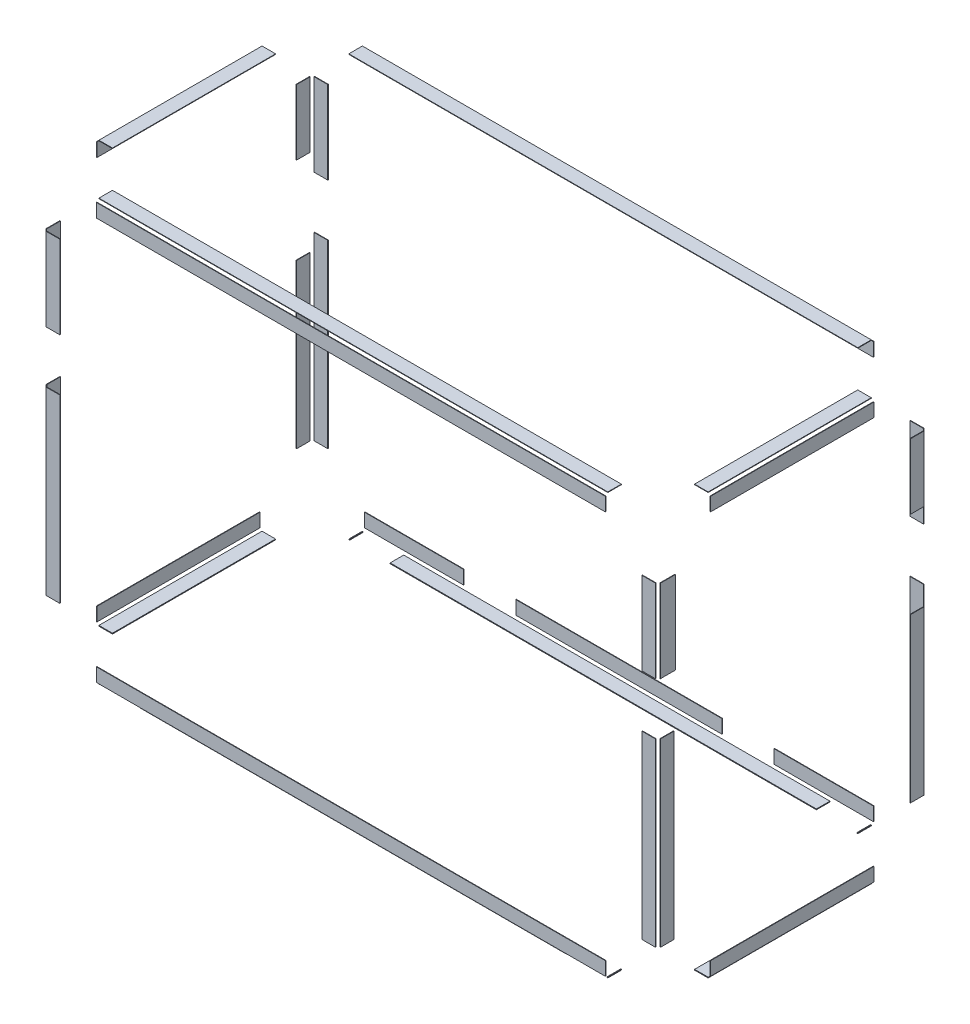
SolidWorks part; units mm, degrees
ref_plane "Front Plane" through (0, 0, 0) normal (0, 0, 1) x (1, 0, 0)
ref_plane "Top Plane" through (0, 0, 0) normal (0, 1, 0) x (1, 0, 0)
ref_plane "Right Plane" through (0, 0, 0) normal (1, 0, 0) x (0, 0, -1)
sketch "Sketch1" plane through (965.8572, 0, 0) normal (1, 0, 0) x (0, 0, -1)
  line L1 (-242.2862, 651.1987) -> (264.3978, 651.1987)
  line L2 (-242.2862, 651.1987) -> (-242.2862, 609.0982)
  line L3 (-242.2862, 609.0982) -> (264.3978, 609.0982)
  line L4 (264.3978, 651.1987) -> (264.3978, 609.0982)
  line L5 (378.0945, 495.4014) -> (420.195, 495.4014)
  line L6 (378.0945, 495.4014) -> (378.0945, 292.2639)
  line L7 (378.0945, 292.2639) -> (420.195, 292.2639)
  line L8 (420.195, 495.4014) -> (420.195, 292.2639)
  line L9 (-398.655, 495.4014) -> (-351.5479, 495.4014)
  line L10 (-398.655, 495.4014) -> (-398.655, 238.2889)
  line L11 (-398.655, 238.2889) -> (-351.5479, 238.2889)
  line L12 (-351.5479, 495.4014) -> (-351.5479, 238.2889)
  line L13 (-398.0835, 76.3639) -> (-355.983, 76.3639)
  line L14 (-398.0835, 76.3639) -> (-398.0835, -484.1046)
  line L15 (-398.0835, -484.1046) -> (-355.983, -484.1046)
  line L16 (-355.983, 76.3639) -> (-355.983, -484.1046)
  line L17 (-242.2862, -597.8013) -> (264.3978, -597.8013)
  line L18 (-242.2862, -597.8013) -> (-242.2862, -639.9018)
  line L19 (-242.2862, -639.9018) -> (264.3978, -639.9018)
  line L20 (264.3978, -597.8013) -> (264.3978, -639.9018)
  line L21 (378.0945, 22.3889) -> (420.195, 22.3889)
  line L22 (378.0945, 22.3889) -> (378.0945, -484.1046)
  line L23 (378.0945, -484.1046) -> (420.195, -484.1046)
  line L24 (420.195, 22.3889) -> (420.195, -484.1046)
extrude "Boss-Extrude1" add sketch "Sketch1" along normal blind 1.5875
sketch "Sketch2" plane through (0, 0, 404.2112) normal (0, 0, 1) x (1, 0, 0)
  line L1 (-776.5738, 605.6529) -> (-776.5738, 651.7702) construction
  line L2 (-776.5738, 651.1987) -> (803.9322, 651.1987)
  line L3 (-776.5738, 651.1987) -> (-776.5738, 609.0982)
  line L4 (-776.5738, 609.0982) -> (803.9322, 609.0982)
  line L9 (803.9322, 651.1987) -> (803.9322, 609.0982)
  line L10 (911.5012, 651.1987) -> (-884.1428, 651.1987) construction
  line L11 (803.9322, 651.7702) -> (803.9322, 605.6529) construction
  line L12 (911.5012, 609.0982) -> (-884.1428, 609.0982) construction
  line L15 (-776.5738, -640.4733) -> (-776.5738, -594.3561) construction
  line L16 (-776.5738, -597.8013) -> (803.9322, -597.8013)
  line L17 (-776.5738, -597.8013) -> (-776.5738, -639.9018)
  line L18 (-776.5738, -639.9018) -> (803.9322, -639.9018)
  line L20 (917.629, -646.0296) -> (917.629, 657.3264) construction
  line L21 (917.629, 495.4014) -> (959.7295, 495.4014)
  line L22 (917.629, 495.4014) -> (917.629, 238.2889)
  line L23 (917.629, 238.2889) -> (959.7295, 238.2889)
  line L24 (959.7295, 495.4014) -> (959.7295, 238.2889)
  line L25 (914.1837, 495.4014) -> (960.301, 495.4014) construction
  line L26 (960.301, 238.2889) -> (913.1939, 238.2889) construction
  line L27 (959.7295, -646.0296) -> (959.7295, 657.3264) construction
  line L28 (913.1939, 76.3639) -> (960.301, 76.3639) construction
  line L29 (917.629, 76.3639) -> (959.7295, 76.3639)
  line L30 (917.629, 76.3639) -> (917.629, -484.1046)
  line L31 (917.629, -484.1046) -> (959.7295, -484.1046)
  line L32 (959.7295, 76.3639) -> (959.7295, -484.1046)
  line L33 (960.301, -484.1046) -> (914.1837, -484.1046) construction
  line L35 (803.9322, -597.8013) -> (803.9322, -639.9018)
  line L36 (911.5012, -597.8013) -> (-884.1428, -597.8013) construction
  line L37 (911.5012, -639.9018) -> (-884.1428, -639.9018) construction
  line L38 (803.9322, -594.3561) -> (803.9322, -640.4733) construction
  line L54 (-932.9425, 76.3639) -> (-885.8354, 76.3639) construction
  line L55 (-932.371, 76.3639) -> (-890.2705, 76.3639)
  line L56 (-932.371, 76.3639) -> (-932.371, -484.1046)
  line L57 (-932.371, -484.1046) -> (-890.2705, -484.1046)
  line L58 (-890.2705, 76.3639) -> (-890.2705, -484.1046)
  line L59 (-932.371, -646.0296) -> (-932.371, 657.3264) construction
  line L60 (-890.2705, -646.0296) -> (-890.2705, 657.3264) construction
  line L61 (-886.8253, -484.1046) -> (-932.9425, -484.1046) construction
  line L62 (-932.9425, 495.4014) -> (-886.8253, 495.4014) construction
  line L63 (-932.371, 495.4014) -> (-890.2705, 495.4014)
  line L64 (-932.371, 495.4014) -> (-932.371, 238.2889)
  line L65 (-932.371, 238.2889) -> (-890.2705, 238.2889)
  line L66 (-890.2705, 495.4014) -> (-890.2705, 238.2889)
  line L67 (-885.8354, 238.2889) -> (-932.9425, 238.2889) construction
extrude "Boss-Extrude2" add sketch "Sketch2" along normal blind 1.5875 separate body
sketch "Sketch3" plane through (-938.4988, 0, 0) normal (-1, 0, 0) x (0, 0, 1)
  line L0 (242.2862, 651.1987) -> (242.2862, 609.0982) construction
  line L1 (-264.3978, 651.1987) -> (242.2862, 651.1987)
  line L2 (-264.3978, 651.1987) -> (-264.3978, 609.0982)
  line L3 (-264.3978, 609.0982) -> (242.2862, 609.0982)
  line L4 (242.2862, 651.1987) -> (242.2862, 609.0982)
  line L5 (242.2862, 609.0982) -> (242.2862, 651.1987) construction
  line L7 (355.983, 495.4014) -> (398.655, 495.4014)
  line L8 (355.983, 495.4014) -> (355.983, 238.2889)
  line L9 (355.983, 238.2889) -> (398.655, 238.2889)
  line L10 (398.655, 495.4014) -> (398.655, 238.2889)
  line L11 (355.983, 76.3639) -> (398.0835, 76.3639)
  line L12 (355.983, 76.3639) -> (355.983, -484.1046)
  line L13 (355.983, -484.1046) -> (398.0835, -484.1046)
  line L14 (398.0835, 76.3639) -> (398.0835, -484.1046)
  line L15 (-264.3978, -597.8013) -> (242.2862, -597.8013)
  line L16 (-264.3978, -597.8013) -> (-264.3978, -639.9018)
  line L17 (-264.3978, -639.9018) -> (242.2862, -639.9018)
  line L18 (242.2862, -597.8013) -> (242.2862, -639.9018)
  line L19 (-420.195, 22.3889) -> (-378.0945, 22.3889)
  line L20 (-420.195, 22.3889) -> (-420.195, -484.1046)
  line L21 (-420.195, -484.1046) -> (-378.0945, -484.1046)
  line L22 (-378.0945, 22.3889) -> (-378.0945, -484.1046)
  line L23 (-420.195, 495.4014) -> (-378.0945, 495.4014)
  line L24 (-420.195, 495.4014) -> (-420.195, 292.2639)
  line L25 (-420.195, 292.2639) -> (-378.0945, 292.2639)
  line L26 (-378.0945, 495.4014) -> (-378.0945, 292.2639)
extrude "Boss-Extrude3" add sketch "Sketch3" along normal blind 1.5875 separate body
sketch "Sketch5" plane through (0, 0, -426.3228) normal (0, 0, -1) x (-1, 0, 0)
  line L0 (-495.6417, 651.7702) -> (-495.6417, 604.6631) construction
  line L1 (-803.9322, 651.1987) -> (-495.6417, 651.1987)
  line L2 (-803.9322, 651.1987) -> (-803.9322, 609.0982)
  line L3 (-803.9322, 609.0982) -> (-495.6417, 609.0982)
  line L4 (-495.6417, 651.1987) -> (-495.6417, 609.0982)
  line L5 (-911.5012, 609.0982) -> (-441.8572, 609.0982) construction
  line L6 (-803.9322, 651.1987) -> (776.5738, 651.1987) construction
  line L7 (-333.7167, 651.1987) -> (306.3583, 651.1987)
  line L8 (-333.7167, 651.1987) -> (-333.7167, 609.0982)
  line L9 (-333.7167, 609.0982) -> (306.3583, 609.0982)
  line L10 (306.3583, 651.1987) -> (306.3583, 609.0982)
  line L11 (-333.7167, 604.6631) -> (-333.7167, 651.7702) construction
  line L12 (306.3583, 651.7702) -> (306.3583, 604.6631) construction
  line L13 (468.2833, 604.6631) -> (468.2833, 651.7702) construction
  line L14 (468.2833, 651.1987) -> (776.5738, 651.1987)
  line L15 (468.2833, 651.1987) -> (468.2833, 609.0982)
  line L16 (468.2833, 609.0982) -> (776.5738, 609.0982)
  line L17 (776.5738, 651.1987) -> (776.5738, 609.0982)
  line L18 (414.4988, 651.1987) -> (884.1428, 651.1987) construction
  line L19 (-803.9322, -597.8013) -> (776.5738, -597.8013) construction
  line L20 (890.2705, 495.4014) -> (932.371, 495.4014)
  line L21 (890.2705, 495.4014) -> (890.2705, 238.2889)
  line L22 (890.2705, 238.2889) -> (932.371, 238.2889)
  line L23 (932.371, 495.4014) -> (932.371, 238.2889)
  line L24 (890.2705, 76.3639) -> (932.371, 76.3639)
  line L25 (890.2705, 76.3639) -> (890.2705, -484.1046)
  line L26 (890.2705, -484.1046) -> (932.371, -484.1046)
  line L27 (932.371, 76.3639) -> (932.371, -484.1046)
  line L28 (468.2833, -597.8013) -> (776.5738, -597.8013)
  line L29 (468.2833, -597.8013) -> (468.2833, -639.9018)
  line L30 (468.2833, -639.9018) -> (776.5738, -639.9018)
  line L31 (776.5738, -597.8013) -> (776.5738, -639.9018)
  line L32 (468.2833, -640.4733) -> (468.2833, -593.3662) construction
  line L33 (-333.7167, -640.4733) -> (-333.7167, -593.3662) construction
  line L34 (-333.7167, -597.8013) -> (306.3583, -597.8013)
  line L35 (-333.7167, -597.8013) -> (-333.7167, -639.9018)
  line L36 (-333.7167, -639.9018) -> (306.3583, -639.9018)
  line L37 (306.3583, -597.8013) -> (306.3583, -639.9018)
  line L38 (776.5738, -639.9018) -> (-803.9322, -639.9018) construction
  line L39 (306.3583, -593.3662) -> (306.3583, -640.4733) construction
  line L40 (-803.9322, -639.9018) -> (-803.9322, -597.8013) construction
  line L41 (-803.9322, -597.8013) -> (-495.6417, -597.8013)
  line L42 (-803.9322, -597.8013) -> (-803.9322, -639.9018)
  line L43 (-803.9322, -639.9018) -> (-495.6417, -639.9018)
  line L44 (-495.6417, -597.8013) -> (-495.6417, -639.9018)
  line L45 (-495.6417, -593.3662) -> (-495.6417, -640.4733) construction
  line L46 (414.4988, -639.9018) -> (884.1428, -639.9018) construction
  line L47 (-959.7295, 495.4014) -> (-917.629, 495.4014) construction
  line L48 (-959.7295, 495.4014) -> (-917.629, 495.4014)
  line L49 (-959.7295, 495.4014) -> (-959.7295, 238.2889)
  line L50 (-959.7295, 238.2889) -> (-917.629, 238.2889)
  line L51 (-917.629, 495.4014) -> (-917.629, 238.2889)
  line L52 (-959.7295, 238.2889) -> (-959.7295, 495.4014) construction
  line L54 (-959.7295, 76.3639) -> (-917.629, 76.3639)
  line L55 (-959.7295, 76.3639) -> (-959.7295, -484.1046)
  line L56 (-959.7295, -484.1046) -> (-917.629, -484.1046)
  line L57 (-917.629, 76.3639) -> (-917.629, -484.1046)
extrude "Boss-Extrude4" add sketch "Sketch5" along normal blind 1.5875 separate body
sketch "Sketch6" plane through (0, 657.3264, 0) normal (0, 1, 0) x (1, 0, 0)
  line L0 (-776.5738, 374.6493) -> (-776.5738, 420.7665) construction
  line L1 (-776.5738, 420.195) -> (803.9322, 420.195)
  line L2 (-776.5738, 420.195) -> (-776.5738, 378.0945)
  line L3 (-776.5738, 378.0945) -> (803.9322, 378.0945)
  line L4 (803.9322, 420.195) -> (803.9322, 378.0945)
  line L5 (-414.4988, 420.195) -> (-884.1428, 420.195) construction
  line L6 (803.9322, 420.7665) -> (803.9322, 374.6493) construction
  line L7 (911.5012, 378.0945) -> (441.8572, 378.0945) construction
  line L8 (917.629, 371.9668) -> (917.629, -349.8552) construction
  line L9 (917.629, 264.3978) -> (959.7295, 264.3978)
  line L10 (917.629, 264.3978) -> (917.629, -242.2862)
  line L11 (917.629, -242.2862) -> (959.7295, -242.2862)
  line L12 (959.7295, 264.3978) -> (959.7295, -242.2862)
  line L13 (914.1837, 264.3978) -> (960.301, 264.3978) construction
  line L14 (960.301, -242.2862) -> (914.1837, -242.2862) construction
  line L15 (959.7295, 371.9668) -> (959.7295, -349.8552) construction
  line L16 (-776.5738, -398.655) -> (-776.5738, -352.5377) construction
  line L17 (-776.5738, -355.983) -> (803.9322, -355.983)
  line L18 (-776.5738, -355.983) -> (-776.5738, -398.0835)
  line L19 (-776.5738, -398.0835) -> (803.9322, -398.0835)
  line L20 (803.9322, -355.983) -> (803.9322, -398.0835)
  line L21 (911.5012, -355.983) -> (-884.1428, -355.983) construction
  line L22 (803.9322, -352.5377) -> (803.9322, -398.655) construction
  line L23 (911.5012, -398.0835) -> (-884.1428, -398.0835) construction
  line L24 (-932.371, 371.9668) -> (-932.371, -349.8552) construction
  line L25 (-932.371, 264.3978) -> (-890.2705, 264.3978)
  line L26 (-932.371, 264.3978) -> (-932.371, -242.2862)
  line L27 (-932.371, -242.2862) -> (-890.2705, -242.2862)
  line L28 (-890.2705, 264.3978) -> (-890.2705, -242.2862)
  line L29 (-932.9425, 264.3978) -> (-886.8253, 264.3978) construction
  line L30 (-890.2705, 371.9668) -> (-890.2705, -349.8552) construction
  line L31 (-886.8253, -242.2862) -> (-932.9425, -242.2862) construction
extrude "Boss-Extrude5" add sketch "Sketch6" along normal blind 1.5875 separate body
sketch "Sketch7" plane through (0, -646.0296, 0) normal (0, -1, 0) x (1, 0, 0)
  line L0 (803.9322, 355.983) -> (-776.5738, 355.983) construction
  line L1 (-776.5738, 398.0835) -> (-774.5008, 398.0835)
  line L2 (-776.5738, 398.0835) -> (-776.5738, 355.983)
  line L3 (-776.5738, 355.983) -> (-774.5008, 355.983)
  line L4 (-774.5008, 398.0835) -> (-774.5008, 355.983)
  line L5 (911.5012, 355.983) -> (-884.1428, 355.983) construction
  line L6 (-776.5738, 398.0835) -> (803.9322, 398.0835) construction
  line L7 (-648.1408, 398.0835) -> (675.4992, 398.0835)
  line L8 (-648.1408, 398.0835) -> (-648.1408, 355.983)
  line L9 (-648.1408, 355.983) -> (675.4992, 355.983)
  line L10 (675.4992, 398.0835) -> (675.4992, 355.983)
  line L11 (-648.1408, 348.5453) -> (-648.1408, 399.2112) construction
  line L12 (675.4992, 399.2112) -> (675.4992, 348.5453) construction
  line L13 (801.8592, 348.5453) -> (801.8592, 399.2112) construction
  line L14 (803.9322, 398.0835) -> (801.8592, 398.0835)
  line L15 (803.9322, 398.0835) -> (803.9322, 355.983)
  line L16 (803.9322, 355.983) -> (801.8592, 355.983)
  line L17 (801.8592, 398.0835) -> (801.8592, 355.983)
  line L18 (803.9322, -420.195) -> (-776.5738, -420.195) construction
  line L19 (917.629, 242.2862) -> (959.7295, 242.2862)
  line L20 (917.629, 242.2862) -> (917.629, -264.3978)
  line L21 (917.629, -264.3978) -> (959.7295, -264.3978)
  line L22 (959.7295, 242.2862) -> (959.7295, -264.3978)
  line L23 (803.9322, -378.0945) -> (801.8592, -378.0945)
  line L24 (803.9322, -378.0945) -> (803.9322, -420.195)
  line L25 (803.9322, -420.195) -> (801.8592, -420.195)
  line L26 (801.8592, -378.0945) -> (801.8592, -420.195)
  line L27 (801.8592, -421.3228) -> (801.8592, -370.6568) construction
  line L28 (-776.5738, -378.0945) -> (803.9322, -378.0945) construction
  line L29 (675.4992, -378.0945) -> (-648.1408, -378.0945)
  line L30 (675.4992, -378.0945) -> (675.4992, -420.195)
  line L31 (675.4992, -420.195) -> (-648.1408, -420.195)
  line L32 (-648.1408, -378.0945) -> (-648.1408, -420.195)
  line L33 (675.4992, -370.6568) -> (675.4992, -421.3228) construction
  line L34 (-414.4988, -420.195) -> (-884.1428, -420.195) construction
  line L35 (-774.5008, -370.6568) -> (-774.5008, -421.3228) construction
  line L36 (-776.5738, -378.0945) -> (-774.5008, -378.0945)
  line L37 (-776.5738, -378.0945) -> (-776.5738, -420.195)
  line L38 (-776.5738, -420.195) -> (-774.5008, -420.195)
  line L39 (-774.5008, -378.0945) -> (-774.5008, -420.195)
  line L41 (-932.371, 242.2862) -> (-890.2705, 242.2862)
  line L42 (-932.371, 242.2862) -> (-932.371, -264.3978)
  line L43 (-932.371, -264.3978) -> (-890.2705, -264.3978)
  line L44 (-890.2705, 242.2862) -> (-890.2705, -264.3978)
extrude "Boss-Extrude6" add sketch "Sketch7" along normal blind 2.36 separate body
